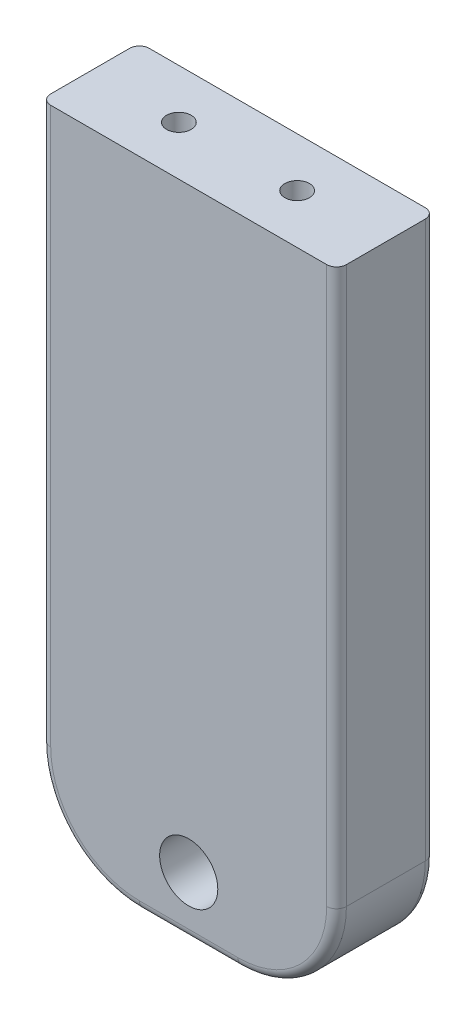
SolidWorks part; units mm, degrees
ref_plane "Front Plane" through (0, 0, 0) normal (0, 0, 1) x (1, 0, 0)
ref_plane "Top Plane" through (0, 0, 0) normal (0, 1, 0) x (1, 0, 0)
ref_plane "Right Plane" through (0, 0, 0) normal (1, 0, 0) x (0, 0, -1)
sketch "Sketch1" plane through (0, 0, 0) normal (0, 0, 1) x (1, 0, 0)
  line L1 (-15, 33.2) -> (15, 33.2)
  line L2 (-15, 33.2) -> (-15, -33.2)
  line L3 (-15, -33.2) -> (15, -33.2)
  line L4 (15, 33.2) -> (15, -33.2)
  line L5 (-15, 33.2) -> (15, -33.2) construction
  line L6 (-15, -33.2) -> (15, 33.2) construction
  point P0 (0, 0)
  dimension "D1" = 30
  dimension "D2" = 66.4
extrude "Boss-Extrude1" add sketch "Sketch1" along normal mid plane 10 contours L1 L4 L3 L2
hole_wizard "Ø6.0mm Dowel Hole1" positions "Sketch2" profile "Sketch3" hole size "Ø6.0" standard "ANSI Metric" end condition through all
sketch "Sketch2" plane through (0, 0, 5) normal (0, 0, 1) x (1, 0, 0)
  line L0 (-15, -33.2) -> (15, -33.2) construction
  point P0 (0, -27.2)
  dimension "D1" = 6
sketch "Sketch3" plane through (0, -27.2, 5) normal (1, 0, 0) x (0, -1, 0)
  line L0 (0, 0) -> (0, 10)
  line L1 (0, 10) -> (2.95, 10)
  line L2 (2.95, 10) -> (2.95, 0)
  line L5 (2.95, 0) -> (0, 0)
  line L11 (0, -6.35) -> (0, 107.95) construction
  dimension "Thru Hole Dia." = 5.9
  dimension "Thru Hole Depth" = 10
hole_wizard "M3x0.5 Tapped Hole1" positions "Sketch4" profile "Sketch6" tap size "M3x0.5" standard "ANSI Metric"
sketch "Sketch4" plane through (0, 33.2, 0) normal (0, 1, 0) x (1, 0, 0)
  line L0 (-6, 0) -> (6, 0)
  point P0 (-6, 0)
  point P2 (6, 0)
  dimension "D1" = 12
  dimension "D2" = 6
sketch "Sketch6" plane through (-6, 33.2, 0) normal (1, 0, 0) x (0, 0, 1)
  line L0 (0, 0) -> (0, 21.7511)
  line L1 (0, 21.7511) -> (1.25, 21)
  line L2 (1.25, 21) -> (1.25, 0)
  line L5 (1.25, 0) -> (0, 0)
  line L10 (0, 21.7511) -> (-1.25, 21) construction
  line L11 (0, -6.35) -> (0, 107.95) construction
  dimension "Tap Drill Dia." = 2.5
  dimension "Tap Drill Depth" = 21
  dimension "Drill Angle" = 118
cosmetic thread "Hole Thread1" parameters "D1"=6, "D2"=3
cosmetic thread "Hole Thread2" parameters "D1"=6, "D2"=3
fillet "Fillet1" radius 10 2 edges at (-15, -33.2, 0) (15, -33.2, 0)
fillet "Fillet2" radius 1 10 edges at (-15, 5, -5) (-12.0711, -30.2711, -5) (12.0711, -30.2711, -5) (15, 5, 5) (12.0711, -30.2711, 5) (-12.0711, -30.2711, 5) (-15, 5, 5) (15, 5, -5) (0, -33.2, 5) (0, -33.2, -5)
